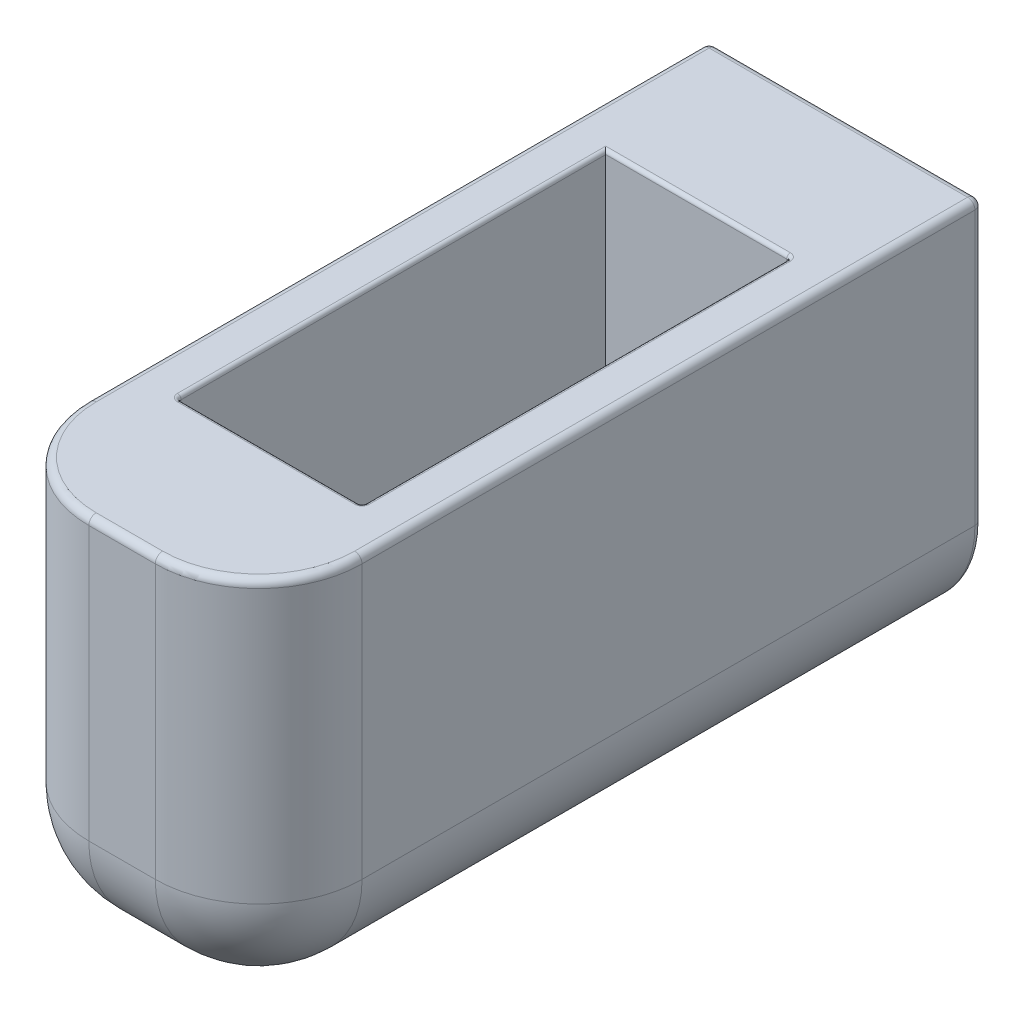
SolidWorks part; units mm, degrees
material "ABS"
ref_plane "Plan de face" through (0, 0, 0) normal (0, 0, 1) x (1, 0, 0)
ref_plane "Plan de dessus" through (0, 0, 0) normal (0, 1, 0) x (1, 0, 0)
ref_plane "Plan de droite" through (0, 0, 0) normal (1, 0, 0) x (0, 0, -1)
sketch "Esquisse1" plane through (0, 0, 0) normal (0, 0, 1) x (1, 0, 0)
  line L0 (0, 0) -> (3, 0)
  line L1 (3, 0) -> (3, -23)
  line L2 (3, -23) -> (15.5, -23)
  line L3 (15.5, -23) -> (15.5, 0)
  line L4 (15.5, 0) -> (18.5, 0)
  line L5 (18.5, 0) -> (18.5, -26)
  line L6 (18.5, -26) -> (0, -26)
  line L7 (0, -26) -> (0, 0)
  dimension "D1" = 18.5
  dimension "D2" = 3
  dimension "D3" = 3
  dimension "D4" = 23
  dimension "D5" = 26
extrude "Boss.-Extru.1" add sketch "Esquisse1" along normal blind 29
sketch "Esquisse2" plane through (0, 0, 0) normal (0, 0, -1) x (-1, 0, 0)
  line L1 (0, -26) -> (-18.5, -26)
  line L2 (0, -26) -> (0, 0)
  line L3 (0, 0) -> (-18.5, 0)
  line L4 (-18.5, -26) -> (-18.5, 0)
extrude "Boss.-Extru.2" add sketch "Esquisse2" along normal blind 10
sketch "Esquisse3" plane through (0, 0, 29) normal (0, 0, 1) x (1, 0, 0)
  line L1 (0, -26) -> (18.5, -26)
  line L2 (0, -26) -> (0, 0)
  line L3 (0, 0) -> (18.5, 0)
  line L4 (18.5, -26) -> (18.5, 0)
extrude "Boss.-Extru.3" add sketch "Esquisse3" along normal blind 10
fillet "Congé3" radius 7 1 edges at (9.25, -26, 39)
sketch "Esquisse7" plane through (0, 0, 0) normal (0, 1, 0) x (1, 0, 0)
  line L0 (9.25, -39) -> (9.25, 10) construction
  line L1 (18.5, -39) -> (0, -39) construction
  line L2 (0, 10) -> (18.5, 10) construction
  point P7 (9.25, 10)
fillet "Congé4" radius 7 3 edges at (18.5, -9.5, 39) (18.5, -23.9497, 36.9497) (18.5, -26, 11)
fillet "Congé5" radius 7 3 edges at (0, -9.5, 39) (0, -23.9497, 36.9497) (0, -26, 11)
fillet "Congé6" radius 0.5 5 edges at (18.5, -9.5, -10) (16.4497, -23.9497, -10) (0, -9.5, -10) (2.0503, -23.9497, -10) (9.25, -26, -10)
fillet "Congé7" radius 0.5 8 edges at (0.1464, 0, -9.8536) (0, 0, 11.25) (2.0503, 0, 36.9497) (9.25, 0, 39) (16.4497, 0, 36.9497) (18.5, 0, 11.25) (18.3536, 0, -9.8536) (9.25, 0, -10)
fillet "Congé8" radius 0.25 11 edges at (15.5, -11.5, 29) (9.25, -23, 29) (9.25, 0, 29) (3, -11.5, 29) (3, -23, 14.5) (3, 0, 14.5) (15.5, -23, 14.5) (15.5, 0, 14.5) (9.25, 0, 0) (15.5, -11.5, 0) (9.25, -23, 0)
